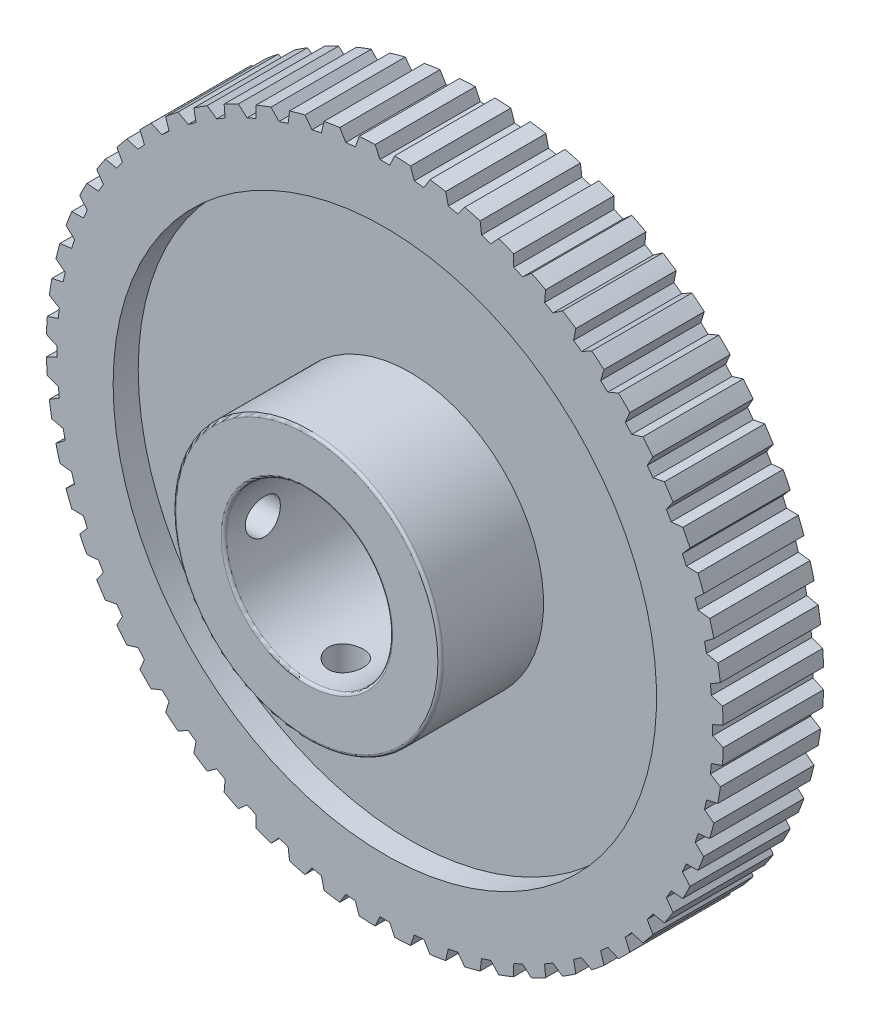
SolidWorks part; units mm, degrees
ref_plane "Front Plane" through (0, 0, 0) normal (0, 0, 1) x (1, 0, 0)
ref_plane "Top Plane" through (0, 0, 0) normal (0, 1, 0) x (1, 0, 0)
ref_plane "Right Plane" through (0, 0, 0) normal (1, 0, 0) x (0, 0, -1)
sketch "Sketch1" plane through (0, 0, 0) normal (0, 0, 1) x (1, 0, 0)
  line L0 (-1.2827, 48.006) -> (-0.6905, 46.736)
  line L1 (-0.6905, 46.736) -> (0.6905, 46.736)
  line L2 (0.6905, 46.736) -> (1.2827, 48.006)
  line L3 (-1.2827, 48.006) -> (1.2827, 48.006)
  line L4 (0, 0) -> (0, 46.736) construction
  line L5 (0, 46.736) -> (0, 49.022) construction
  circle A0 centre (0, 0) radius 48.514 construction
  circle A1 centre (0, 0) radius 48.26 construction
  circle A2 centre (0, 0) radius 48.0231 construction
  point P6 (0, 48.006)
  point P11 (0, 48.514)
  point P13 (0, 48.26)
  point P14 (0, 48.0231)
  dimension "D1" = 1.016
  dimension "D2" = 0.508
sketch "Sketch2" plane through (0, 0, 0) normal (1, 0, 0) x (0, 0, -1)
  line L0 (-12.7, 11.85) -> (12.7, 11.85)
  line L1 (-12.7, 11.85) -> (-12.7, 19.05)
  line L2 (-12.7, 19.05) -> (-1.6002, 19.05)
  line L3 (-1.6002, 19.05) -> (-1.6002, 48.26)
  line L9 (12.7, 48.26) -> (12.7, 11.85)
  line L10 (-12.7, 0) -> (12.7, 0) construction
  line L16 (-1.6002, 48.26) -> (12.7, 48.26)
  point P25 (12.7, 0)
  point P26 (-1.6002, 0)
  dimension "OA" = 25.4
  dimension "Bore" = 23.7
  dimension "Hub Dia" = 38.1
  dimension "Outside Width" = 14.3002
revolve "Revolve1" add sketch "Sketch2" angle 360 mid plane about L10
sketch "Sketch3" plane through (0, 0, 0) normal (0, 0, 1) x (1, 0, 0)
  line L0 (-0.6905, 46.736) -> (0.6905, 46.736) construction
  line L1 (0.6905, 46.736) -> (1.2827, 48.006) construction
  line L2 (-1.2827, 48.006) -> (-0.6905, 46.736) construction
  line L3 (-0.6905, 46.736) -> (0.6905, 46.736)
  line L4 (0.6905, 46.736) -> (1.3918, 48.2399)
  line L5 (-1.3918, 48.2399) -> (-0.6905, 46.736)
  circle A2 centre (0, 0) radius 48.26 construction
  arc A3 (1.3918, 48.2399) -> (-1.3918, 48.2399) centre (0, 0) ccw
extrude "Cut-Extrude1" cut sketch "Sketch3" against normal through all from surface at 1.6002 starting at face at (19.05, 0, 1.6002)
pattern_circular "CirPattern1" count 60 over 360 about axis through (0, 0, 0) along (0, 0, 1) of "Cut-Extrude1"
sketch "Sketch4" plane through (0, 0, 0) normal (1, 0, 0) x (0, 0, -1)
  line L0 (-12.7, 0) -> (-1.6002, 0) construction
  line L1 (-12.7, 19.05) -> (-12.7, -19.05) construction
  line L2 (-1.6002, 19.05) -> (-1.6002, -19.05) construction
  circle A0 centre (-7.1501, 0) radius 2.5
  dimension "D1" = 5
extrude "Cut-Extrude2" cut sketch "Sketch4" against normal through all
pattern_circular "CirPattern2" count 2 every 90 about axis through (0, 0, 12.7) along (0, 0, 1) of "Cut-Extrude2"
ref_plane "Plane1" through (0, 0, 7.1501) normal (0, 0, 1) x (1, 0, 0)
sketch "Sketch5" plane through (0, 0, 7.1501) normal (0, 0, 1) x (1, 0, 0)
  line L1 (-17.653, 2.5) -> (-13.247, 2.5)
  line L2 (-18.288, 1.865) -> (-18.288, 0)
  line L3 (-18.288, 0) -> (-12.612, 0) construction
  line L4 (-12.612, 1.865) -> (-12.612, 0)
  line L13 (-11.5833, 2.5) -> (-18.8852, 2.5) construction
  line L23 (-12.612, 0) -> (-18.288, 0)
  line L24 (-18.288, 1.865) -> (-17.653, 2.5)
  line L25 (-13.247, 2.5) -> (-12.612, 1.865)
  circle A0 centre (0, 0) radius 19.05 construction
  circle A1 centre (0, 0) radius 11.85 construction
  point P0 (-18.288, 2.5)
  point P3 (-12.612, 2.5)
  point P4 (-19.05, 0)
  point P6 (-11.85, 0)
  dimension "D1" = 0.762
  dimension "D2" = 0.762
revolve "Revolve2" [suppressed] add sketch "Sketch5" angle 360 mid plane about L3
sketch "Sketch6" [suppressed] plane through (-18.288, 0, 0) normal (-1, 0, 0) x (0, 0, 1)
  line L1 (7.1501, 1.3748) -> (5.9595, 0.6874)
  line L2 (5.9595, 0.6874) -> (5.9595, -0.6874)
  line L3 (5.9595, -0.6874) -> (7.1501, -1.3748)
  line L4 (7.1501, -1.3748) -> (8.3407, -0.6874)
  line L5 (8.3407, -0.6874) -> (8.3407, 0.6874)
  line L6 (8.3407, 0.6874) -> (7.1501, 1.3748)
  circle A0 centre (7.1501, 0) radius 1.1906 construction
  dimension "D1" = 2.5
extrude "Cut-Extrude3" [suppressed] cut sketch "Sketch6" against normal blind 1.524
pattern_circular "CirPattern3" [suppressed] count 2 every 90
fillet "Fillet1" radius 0.381 3 edges at (19.05, 0, 1.6002) (19.05, 0, 12.7) (11.85, 0, 12.7)
sketch "Sketch7" plane through (0, 0, 12.7) normal (0, 0, 1) x (1, 0, 0)
  circle A0 centre (0, 0) radius 19.05
  circle A1 centre (0, 0) radius 38.735
  circle A2 centre (0, 0) radius 19.05 construction
  circle A3 centre (0, 0) radius 48.26 construction
  dimension "D1" = 9.525
sketch "Sketch9" plane through (0, 0, -12.7) normal (0, 0, -1) x (-1, 0, 0)
  circle A0 centre (0, 0) radius 38.735 construction
  circle A1 centre (0, 0) radius 19.05 construction
  circle A2 centre (0, 0) radius 38.735
  circle A3 centre (0, 0) radius 19.05
extrude "Cut-Extrude4" cut sketch "Sketch7" against normal offset from surface (14.6748 mm away) 3.575 up to face at (-19.431, 0, 1.6002) offset beyond the face yes
extrude "Cut-Extrude5" cut sketch "Sketch9" against normal blind 3.575
equation "\"D2@Sketch1\" = \"D1@Sketch1\"/2"
equation "\"D1@Sketch6\" = \"D1@Sketch4\"/2"
